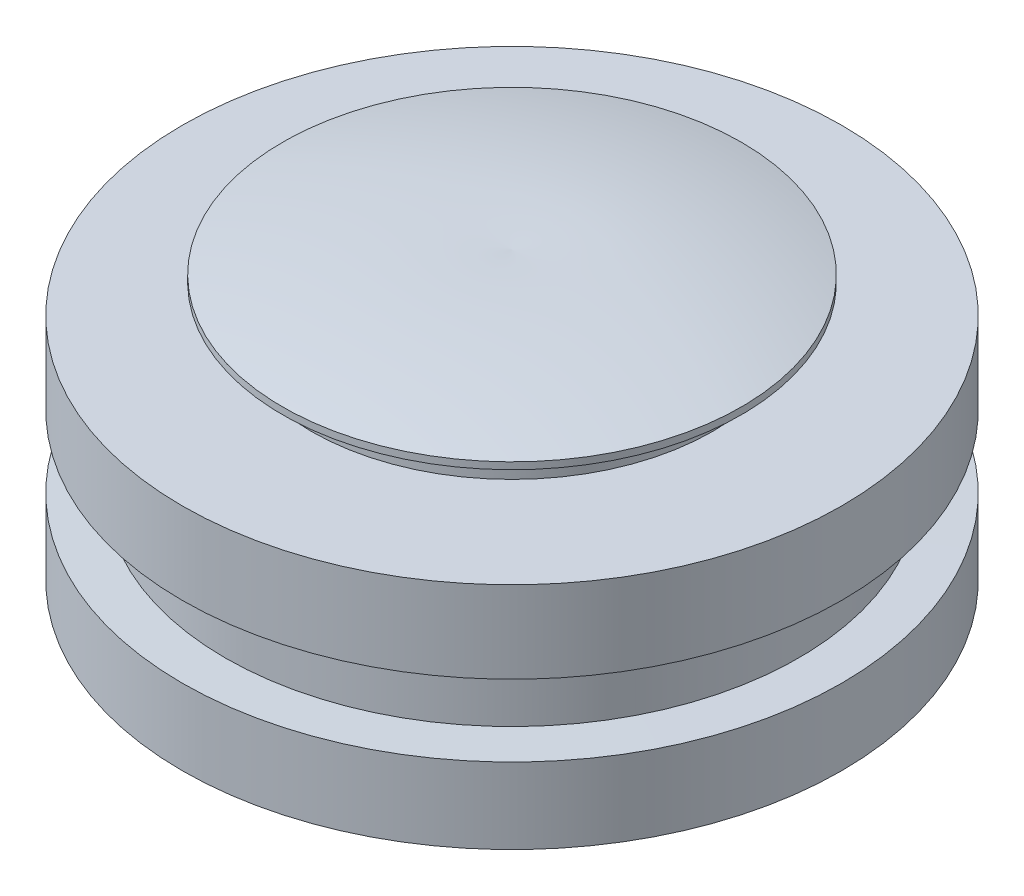
SolidWorks part; units mm, degrees
ref_plane "Спереди" through (0, 0, 0) normal (0, 0, 1) x (1, 0, 0)
ref_plane "Сверху" through (0, 0, 0) normal (0, 1, 0) x (1, 0, 0)
ref_plane "Справа" through (0, 0, 0) normal (1, 0, 0) x (0, 0, -1)
sketch "Эскиз1" plane through (0, 0, 0) normal (0, 0, 1) x (1, 0, 0)
  line L0 (11.5, -2.9822) -> (11.5, -5.6274)
  line L1 (11.5, -5.6274) -> (6, -5.6274)
  line L2 (6, -5.6274) -> (6, 2.3726)
  line L3 (6, 2.3726) -> (0, 3.3726)
  line L4 (0, 3.3726) -> (0, 4.3726)
  line L5 (11.5, -2.9822) -> (10, -2.9712)
  line L6 (10, -2.9712) -> (10, -0.4705)
  line L7 (10, -0.4705) -> (11.5, -0.4815)
  line L8 (11.5, -0.4815) -> (11.5, 2.3726)
  line L9 (11.5, 2.3726) -> (7, 2.3726)
  line L10 (7, 2.3726) -> (7, 3.3726)
  line L11 (7, 3.3726) -> (8, 3.3726)
  line L12 (8, 3.3726) -> (8, 3.6112)
  arc A0 (0, 4.3726) -> (8, 3.6112) centre (1.5661, -21.5802) cw
  dimension "D11" = 26
  dimension "D1" = 11.5
  dimension "D2" = 8
  dimension "D3" = 10
  dimension "D4" = 1
  dimension "D5" = 1
  dimension "D6" = 6
  dimension "D7" = 5.5
  dimension "D8" = 10
  dimension "D9" = 7
  dimension "D10" = 8
  dimension "D12" = 8
  dimension "D13" = 360
  dimension "D14" = 2.5006
revolve "Повернуть1" add sketch "Эскиз1" angle 360 about L4
